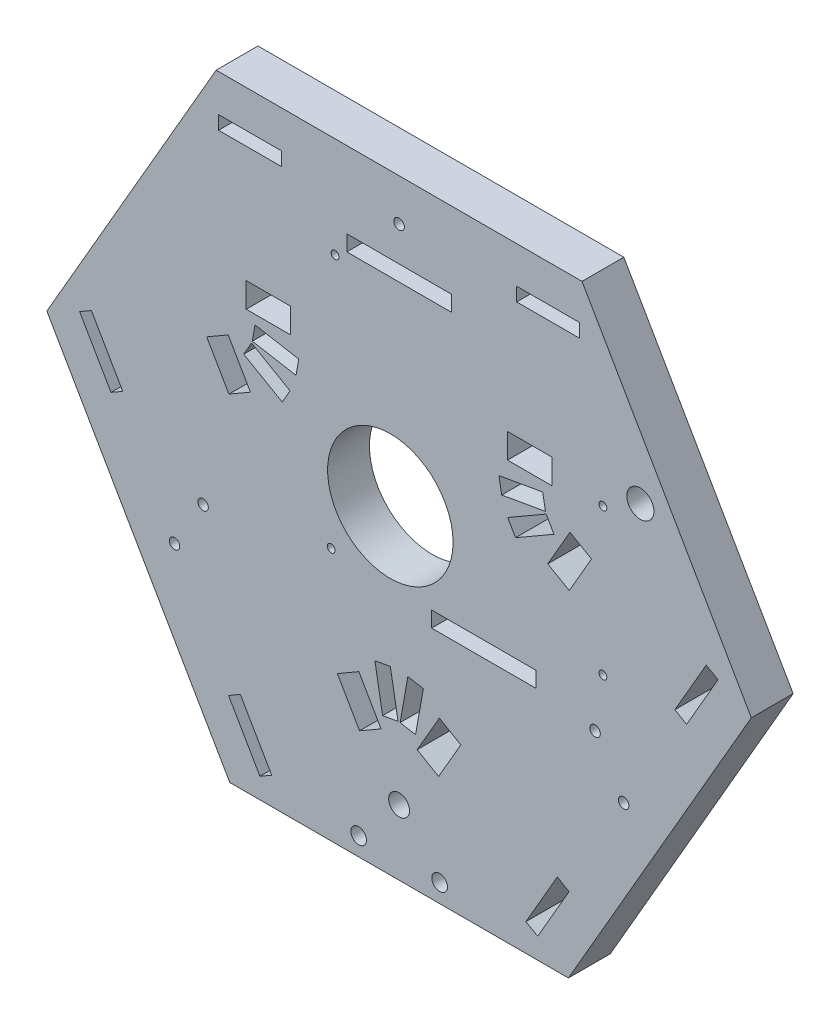
SolidWorks part; units mm, degrees
ref_plane "Plano frontal" through (0, 0, 0) normal (0, 0, 1) x (1, 0, 0)
ref_plane "Plano superior" through (0, 0, 0) normal (0, 1, 0) x (1, 0, 0)
ref_plane "Plano direito" through (0, 0, 0) normal (1, 0, 0) x (0, 0, -1)
sketch "Model" plane through (0, 0, 0) normal (0, 0, 1) x (1, 0, 0)
  line L0 (312.4019, 240.8782) -> (347.4019, 301.5)
  line L1 (347.4019, 301.5) -> (315, 357.6218)
  line L2 (315, 357.6218) -> (245, 357.6218)
  line L3 (245, 357.6218) -> (212.5981, 301.5)
  line L4 (212.5981, 301.5) -> (247.5981, 240.8782)
  line L5 (247.5981, 240.8782) -> (312.4019, 240.8782)
  line L6 (245.4531, 350.4867) -> (257.4531, 350.4867)
  line L7 (245.4531, 347.8867) -> (245.4531, 350.4867)
  line L8 (314.5, 350.5596) -> (302.5, 350.5596)
  line L9 (314.5, 347.9596) -> (314.5, 350.5596)
  line L10 (332.7685, 295.5164) -> (335.0202, 294.2164)
  line L11 (338.7685, 305.9087) -> (341.0202, 304.6087)
  line L12 (310.2721, 256.5432) -> (312.5238, 255.2432)
  line L13 (304.2685, 246.1529) -> (306.5202, 244.8529)
  line L14 (255.6232, 246.0904) -> (253.3716, 244.7904)
  line L15 (249.6232, 256.4827) -> (247.3716, 255.1827)
  line L16 (227.1232, 295.4539) -> (224.8716, 294.1539)
  line L17 (221.1232, 305.8462) -> (218.8716, 304.5462)
  line L18 (221.1232, 305.8462) -> (227.1232, 295.4539)
  line L19 (249.6232, 256.4827) -> (255.6232, 246.0904)
  line L20 (304.2685, 246.1529) -> (310.2721, 256.5432)
  line L21 (332.7685, 295.5164) -> (338.7685, 305.9087)
  line L22 (302.5, 350.5596) -> (302.5, 347.9596)
  line L23 (245.4531, 347.8867) -> (257.4531, 347.8867)
  line L24 (218.8716, 304.5462) -> (224.8716, 294.1539)
  line L25 (247.3716, 255.1827) -> (253.3716, 244.7904)
  line L26 (312.5238, 255.2432) -> (306.5202, 244.8529)
  line L27 (257.4531, 347.8867) -> (257.4531, 350.4867)
  line L28 (302.5, 347.9596) -> (314.5, 347.9596)
  line L29 (335.0202, 294.2164) -> (341.0202, 304.6087)
  line L42 (300.75, 320.8718) -> (309.25, 320.8718)
  line L43 (309.25, 320.8718) -> (309.25, 325.6218)
  line L44 (309.25, 325.6218) -> (300.75, 325.6218)
  line L45 (300.75, 325.6218) -> (300.75, 320.8718)
  line L46 (312.7005, 314.8954) -> (308.4505, 307.5341)
  line L47 (308.4505, 307.5341) -> (312.5641, 305.1591)
  line L48 (312.5641, 305.1591) -> (316.8141, 312.5204)
  line L49 (316.8141, 312.5204) -> (312.7005, 314.8954)
  line L50 (250.75, 320.8718) -> (259.25, 320.8718)
  line L51 (259.25, 320.8718) -> (259.25, 325.6218)
  line L52 (259.25, 325.6218) -> (250.75, 325.6218)
  line L53 (250.75, 325.6218) -> (250.75, 320.8718)
  line L54 (251.5495, 307.5341) -> (247.2995, 314.8954)
  line L55 (247.2995, 314.8954) -> (243.1859, 312.5204)
  line L56 (243.1859, 312.5204) -> (247.4359, 305.1591)
  line L57 (247.4359, 305.1591) -> (251.5495, 307.5341)
  line L58 (272.2995, 271.5941) -> (268.1859, 269.2191)
  line L59 (268.1859, 269.2191) -> (272.4359, 261.8579)
  line L60 (272.4359, 261.8579) -> (276.5495, 264.2329)
  line L61 (287.7005, 271.5941) -> (283.4505, 264.2329)
  line L62 (283.4505, 264.2329) -> (287.5641, 261.8579)
  line L63 (287.5641, 261.8579) -> (291.8141, 269.2191)
  line L64 (291.8141, 269.2191) -> (287.7005, 271.5941)
  line L65 (272.2995, 271.5941) -> (276.5495, 264.2329)
  line L78 (279.8, 267.1) -> (278.324, 275.4709)
  line L79 (278.324, 275.4709) -> (275.3696, 274.9499)
  line L80 (275.3696, 274.9499) -> (276.8456, 266.5791)
  line L81 (276.8456, 266.5791) -> (279.8, 267.1)
  line L82 (281.676, 275.4709) -> (280.2, 267.1)
  line L83 (280.2, 267.1) -> (283.1544, 266.5791)
  line L84 (283.1544, 266.5791) -> (284.6304, 274.9499)
  line L85 (284.6304, 274.9499) -> (281.676, 275.4709)
  line L86 (308.1368, 315.6241) -> (300.7756, 311.3741)
  line L87 (300.7756, 311.3741) -> (302.2756, 308.776)
  line L88 (302.2756, 308.776) -> (309.6368, 313.026)
  line L89 (309.6368, 313.026) -> (308.1368, 315.6241)
  line L90 (299.6291, 314.524) -> (308, 316)
  line L91 (308, 316) -> (307.4791, 318.9544)
  line L92 (307.4791, 318.9544) -> (299.1082, 317.4784)
  line L93 (299.1082, 317.4784) -> (299.6291, 314.524)
  line L94 (251.9071, 316.1604) -> (260.2779, 314.6844)
  line L95 (260.2779, 314.6844) -> (260.7989, 317.6389)
  line L96 (260.7989, 317.6389) -> (252.428, 319.1149)
  line L97 (252.428, 319.1149) -> (251.9071, 316.1604)
  line L98 (259.1315, 311.5346) -> (251.7703, 315.7846)
  line L99 (251.7703, 315.7846) -> (250.2703, 313.1865)
  line L100 (250.2703, 313.1865) -> (257.6315, 308.9365)
  line L101 (257.6315, 308.9365) -> (259.1315, 311.5346)
  line L102 (270, 340) -> (290, 340)
  line L103 (290, 340) -> (290, 343)
  line L104 (290, 343) -> (270, 343)
  line L105 (270, 343) -> (270, 340)
  line L106 (286.2303, 285.771) -> (306.2303, 285.771)
  line L107 (306.2303, 285.771) -> (306.2303, 288.771)
  line L108 (306.2303, 288.771) -> (286.2303, 288.771)
  line L109 (286.2303, 288.771) -> (286.2303, 285.771)
  circle A0 centre (280, 253.3782) radius 2
  circle A1 centre (272.2603, 244.389) radius 1.5
  circle A2 centre (287.7603, 244.389) radius 1.5
  circle A3 centre (242.5, 284.3782) radius 1
  circle A4 centre (317.5, 284.3782) radius 1
  circle A5 centre (267.7505, 338.3824) radius 0.75
  circle A6 centre (267, 289.3782) radius 0.75
  circle A7 centre (319, 294.3782) radius 0.75
  circle A8 centre (319, 322.3782) radius 0.75
  circle A9 centre (280, 349.6218) radius 1
  circle A10 centre (237.0263, 275.1891) radius 1
  circle A11 centre (322.9737, 275.1891) radius 1
  circle A12 centre (326.1596, 326.3628) radius 2.6
  circle A13 centre (278.324, 302.0322) radius 12
  dimension "D1" = 134.8038
  dimension "D2" = 5.2099
  dimension "D3" = 12
  dimension "D4" = 2.6
  dimension "D5" = 5.2122
  dimension "D6" = 12
  dimension "D7" = 2.6
  dimension "D8" = 45
  dimension "D9" = 3.9747
  dimension "D10" = 12
  dimension "D11" = 3.9724
  dimension "D12" = 12
  dimension "D13" = 2.6
  dimension "D14" = 2.6
  dimension "D15" = 45
  dimension "D16" = 3.96
  dimension "D17" = 3.9641
  dimension "D18" = 12
  dimension "D19" = 45.0469
  dimension "D20" = 2.6
  dimension "D21" = 12
  dimension "D22" = 2.6
sketch "Esboço2" plane through (0, 0, 0) normal (0, 0, 1) x (1, 0, 0)
  line L0 (312.4019, 240.8782) -> (347.4019, 301.5)
  line L1 (347.4019, 301.5) -> (315, 357.6218)
  line L2 (315, 357.6218) -> (245, 357.6218)
  line L3 (245, 357.6218) -> (212.5981, 301.5)
  line L4 (212.5981, 301.5) -> (247.5981, 240.8782)
  line L5 (247.5981, 240.8782) -> (312.4019, 240.8782)
  line L6 (245.4531, 350.4867) -> (257.4531, 350.4867)
  line L7 (245.4531, 347.8867) -> (245.4531, 350.4867)
  line L8 (314.5, 350.5596) -> (302.5, 350.5596)
  line L9 (314.5, 347.9596) -> (314.5, 350.5596)
  line L10 (332.7685, 295.5164) -> (335.0202, 294.2164)
  line L11 (338.7685, 305.9087) -> (341.0202, 304.6087)
  line L12 (310.2721, 256.5432) -> (312.5238, 255.2432)
  line L13 (304.2685, 246.1529) -> (306.5202, 244.8529)
  line L14 (255.6232, 246.0904) -> (253.3716, 244.7904)
  line L15 (249.6232, 256.4827) -> (247.3716, 255.1827)
  line L16 (227.1232, 295.4539) -> (224.8716, 294.1539)
  line L17 (221.1232, 305.8462) -> (218.8716, 304.5462)
  line L18 (221.1232, 305.8462) -> (227.1232, 295.4539)
  line L19 (249.6232, 256.4827) -> (255.6232, 246.0904)
  line L20 (304.2685, 246.1529) -> (310.2721, 256.5432)
  line L21 (332.7685, 295.5164) -> (338.7685, 305.9087)
  line L22 (302.5, 350.5596) -> (302.5, 347.9596)
  line L23 (245.4531, 347.8867) -> (257.4531, 347.8867)
  line L24 (218.8716, 304.5462) -> (224.8716, 294.1539)
  line L25 (247.3716, 255.1827) -> (253.3716, 244.7904)
  line L26 (312.5238, 255.2432) -> (306.5202, 244.8529)
  line L27 (257.4531, 347.8867) -> (257.4531, 350.4867)
  line L28 (302.5, 347.9596) -> (314.5, 347.9596)
  line L29 (335.0202, 294.2164) -> (341.0202, 304.6087)
  line L30 (300.75, 320.8718) -> (309.25, 320.8718)
  line L31 (309.25, 320.8718) -> (309.25, 325.6218)
  line L32 (309.25, 325.6218) -> (300.75, 325.6218)
  line L33 (300.75, 325.6218) -> (300.75, 320.8718)
  line L34 (312.7005, 314.8954) -> (308.4505, 307.5341)
  line L35 (308.4505, 307.5341) -> (312.5641, 305.1591)
  line L36 (312.5641, 305.1591) -> (316.8141, 312.5204)
  line L37 (316.8141, 312.5204) -> (312.7005, 314.8954)
  line L38 (250.75, 320.8718) -> (259.25, 320.8718)
  line L39 (259.25, 320.8718) -> (259.25, 325.6218)
  line L40 (259.25, 325.6218) -> (250.75, 325.6218)
  line L41 (250.75, 325.6218) -> (250.75, 320.8718)
  line L42 (251.5495, 307.5341) -> (247.2995, 314.8954)
  line L43 (247.2995, 314.8954) -> (243.1859, 312.5204)
  line L44 (243.1859, 312.5204) -> (247.4359, 305.1591)
  line L45 (247.4359, 305.1591) -> (251.5495, 307.5341)
  line L46 (272.2995, 271.5941) -> (268.1859, 269.2191)
  line L47 (268.1859, 269.2191) -> (272.4359, 261.8579)
  line L48 (272.4359, 261.8579) -> (276.5495, 264.2329)
  line L49 (287.7005, 271.5941) -> (283.4505, 264.2329)
  line L50 (283.4505, 264.2329) -> (287.5641, 261.8579)
  line L51 (287.5641, 261.8579) -> (291.8141, 269.2191)
  line L52 (291.8141, 269.2191) -> (287.7005, 271.5941)
  line L53 (272.2995, 271.5941) -> (276.5495, 264.2329)
  line L54 (279.8, 267.1) -> (278.324, 275.4709)
  line L55 (278.324, 275.4709) -> (275.3696, 274.9499)
  line L56 (275.3696, 274.9499) -> (276.8456, 266.5791)
  line L57 (276.8456, 266.5791) -> (279.8, 267.1)
  line L58 (281.676, 275.4709) -> (280.2, 267.1)
  line L59 (280.2, 267.1) -> (283.1544, 266.5791)
  line L60 (283.1544, 266.5791) -> (284.6304, 274.9499)
  line L61 (284.6304, 274.9499) -> (281.676, 275.4709)
  line L62 (308.1368, 315.6241) -> (300.7756, 311.3741)
  line L63 (300.7756, 311.3741) -> (302.2756, 308.776)
  line L64 (302.2756, 308.776) -> (309.6368, 313.026)
  line L65 (309.6368, 313.026) -> (308.1368, 315.6241)
  line L66 (299.6291, 314.524) -> (308, 316)
  line L67 (308, 316) -> (307.4791, 318.9544)
  line L68 (307.4791, 318.9544) -> (299.1082, 317.4784)
  line L69 (299.1082, 317.4784) -> (299.6291, 314.524)
  line L70 (251.9071, 316.1604) -> (260.2779, 314.6844)
  line L71 (260.2779, 314.6844) -> (260.7989, 317.6389)
  line L72 (260.7989, 317.6389) -> (252.428, 319.1149)
  line L73 (252.428, 319.1149) -> (251.9071, 316.1604)
  line L74 (259.1315, 311.5346) -> (251.7703, 315.7846)
  line L75 (251.7703, 315.7846) -> (250.2703, 313.1865)
  line L76 (250.2703, 313.1865) -> (257.6315, 308.9365)
  line L77 (257.6315, 308.9365) -> (259.1315, 311.5346)
  line L78 (270, 340) -> (290, 340)
  line L79 (290, 340) -> (290, 343)
  line L80 (290, 343) -> (270, 343)
  line L81 (270, 343) -> (270, 340)
  line L82 (286.2303, 285.771) -> (306.2303, 285.771)
  line L83 (306.2303, 285.771) -> (306.2303, 288.771)
  line L84 (306.2303, 288.771) -> (286.2303, 288.771)
  line L85 (286.2303, 288.771) -> (286.2303, 285.771)
  circle A0 centre (280, 253.3782) radius 2
  circle A1 centre (272.2603, 244.389) radius 1.5
  circle A2 centre (287.7603, 244.389) radius 1.5
  circle A3 centre (242.5, 284.3782) radius 1
  circle A4 centre (317.5, 284.3782) radius 1
  circle A5 centre (267.7505, 338.3824) radius 0.75
  circle A6 centre (267, 289.3782) radius 0.75
  circle A7 centre (319, 294.3782) radius 0.75
  circle A8 centre (319, 322.3782) radius 0.75
  circle A9 centre (280, 349.6218) radius 1
  circle A10 centre (237.0263, 275.1891) radius 1
  circle A11 centre (322.9737, 275.1891) radius 1
  circle A12 centre (326.1596, 326.3628) radius 2.6
  circle A13 centre (278.324, 302.0322) radius 12
  dimension "D1" = 134.8038
  dimension "D2" = 5.2099
  dimension "D3" = 12
  dimension "D4" = 2.6
  dimension "D5" = 5.2122
  dimension "D6" = 12
  dimension "D7" = 2.6
  dimension "D8" = 45
  dimension "D9" = 3.9747
  dimension "D10" = 12
  dimension "D11" = 3.9724
  dimension "D12" = 12
  dimension "D13" = 2.6
  dimension "D14" = 2.6
  dimension "D15" = 45
  dimension "D16" = 3.96
  dimension "D17" = 3.9641
  dimension "D18" = 12
  dimension "D19" = 2.6
  dimension "D20" = 45.0469
  dimension "D21" = 12
  dimension "D22" = 2.6
extrude "Ressalto-extrusão1" add sketch "Esboço2" along normal blind 8
